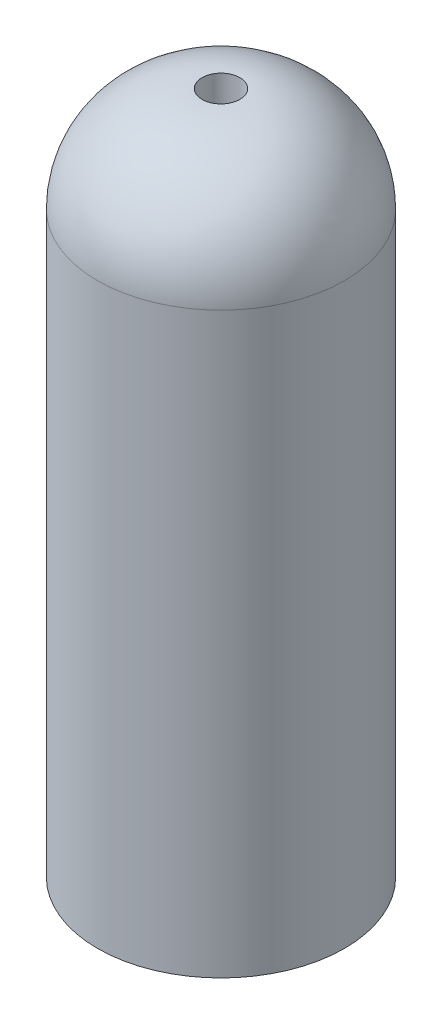
SolidWorks part; units mm, degrees
material "Ferro dúctil"
ref_plane "Plano frontal" through (0, 0, 0) normal (0, 0, 1) x (1, 0, 0)
ref_plane "Plano superior" through (0, 0, 0) normal (0, 1, 0) x (1, 0, 0)
ref_plane "Plano direito" through (0, 0, 0) normal (1, 0, 0) x (0, 0, -1)
sketch "Esboço1" plane through (0, 0, 0) normal (0, 1, 0) x (1, 0, 0)
  circle A0 centre (0, 0) radius 85
  dimension "D1" = 170
extrude "Ressalto-extrusão1" add sketch "Esboço1" along normal blind 500
fillet "Filete1" radius 72 1 edges at (0, 500, 85)
fillet "Filete2" radius 5 1 edges at (0, 0, 85)
sketch "Esboço2" plane through (0, 0, 0) normal (0, -1, 0) x (1, 0, 0)
  circle A0 centre (0, 0) radius 135
  dimension "D1" = 270
extrude "Corte-extrusão1" cut sketch "Esboço2" against normal blind 30
sketch "Esboço7" plane through (0, 30, 0) normal (0, -1, 0) x (1, 0, 0)
  text T0 "CO2\r\n6 Kg\r\n123456" font "Century Gothic" height 15
extrude "Corte-extrusão2" cut sketch "Esboço7" against normal blind 1
sketch "Esboço8" plane through (0, 500, 0) normal (0, 1, 0) x (1, 0, 0)
  circle A0 centre (0, 0) radius 13 construction
  circle A1 centre (0, 0) radius 13
extrude "Corte-extrusão3" cut sketch "Esboço8" against normal blind 20
